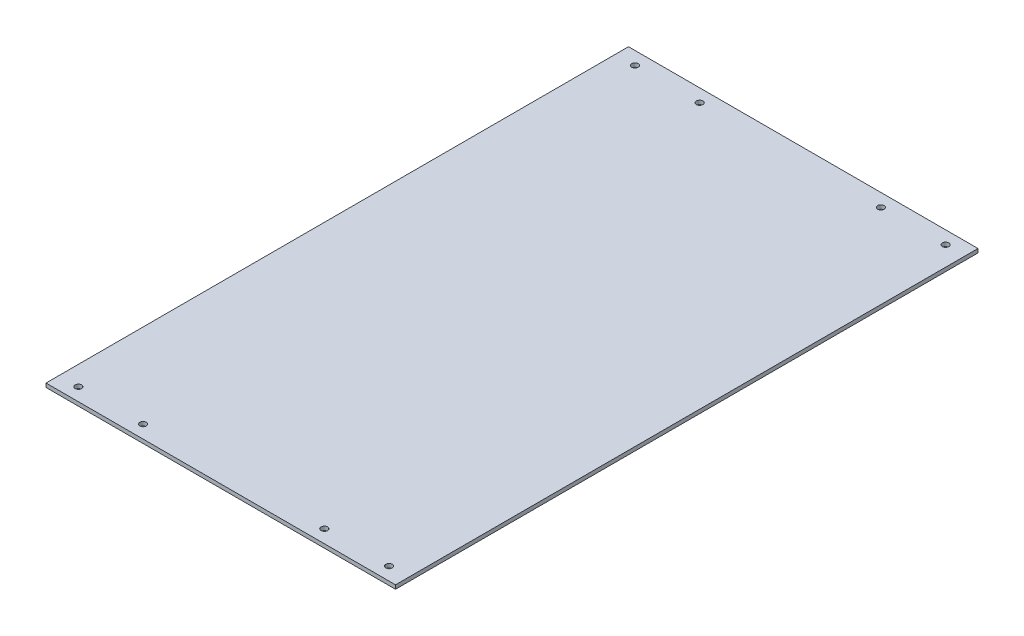
SolidWorks part; units mm, degrees
ref_plane "Front Plane" through (0, 0, 0) normal (0, 0, 1) x (1, 0, 0)
ref_plane "Top Plane" through (0, 0, 0) normal (0, 1, 0) x (1, 0, 0)
ref_plane "Right Plane" through (0, 0, 0) normal (1, 0, 0) x (0, 0, -1)
sketch "Sketch1" plane through (0, 0, 0) normal (0, 0, 1) x (1, 0, 0)
  line L1 (135, -1.5) -> (-135, -1.5)
  line L2 (135, -1.5) -> (135, 1.5)
  line L3 (135, 1.5) -> (-135, 1.5)
  line L4 (-135, -1.5) -> (-135, 1.5)
  line L5 (135, -1.5) -> (-135, 1.5) construction
  line L6 (135, 1.5) -> (-135, -1.5) construction
  point P0 (0, 0)
  dimension "D1" = 270
  dimension "D2" = 3
extrude "Boss-Extrude1" add sketch "Sketch1" against normal blind 450
sketch "Sketch2" plane through (0, 1.5, 0) normal (0, 1, 0) x (1, 0, 0)
  line L0 (135, 450) -> (-135, 450) construction
  line L1 (-135, 450) -> (-135, 0) construction
  line L2 (0, 450) -> (0, 534.5329) construction
  line L3 (135, 225) -> (-348.299, 225) construction
  line L4 (135, 450) -> (135, 0) construction
  circle A0 centre (-120, 440) radius 2.5
  circle A1 centre (-70, 440) radius 2.5
  circle A2 centre (70, 440) radius 2.5
  circle A3 centre (120, 440) radius 2.5
  circle A4 centre (120, 10) radius 2.5
  circle A5 centre (70, 10) radius 2.5
  circle A6 centre (-70, 10) radius 2.5
  circle A7 centre (-120, 10) radius 2.5
  dimension "D1" = 5
  dimension "D4" = 5
  dimension "D6" = 10
  dimension "D2" = 10
  dimension "D3" = 15
  dimension "D5" = 50
extrude "Cut-Extrude1" cut sketch "Sketch2" against normal through all
